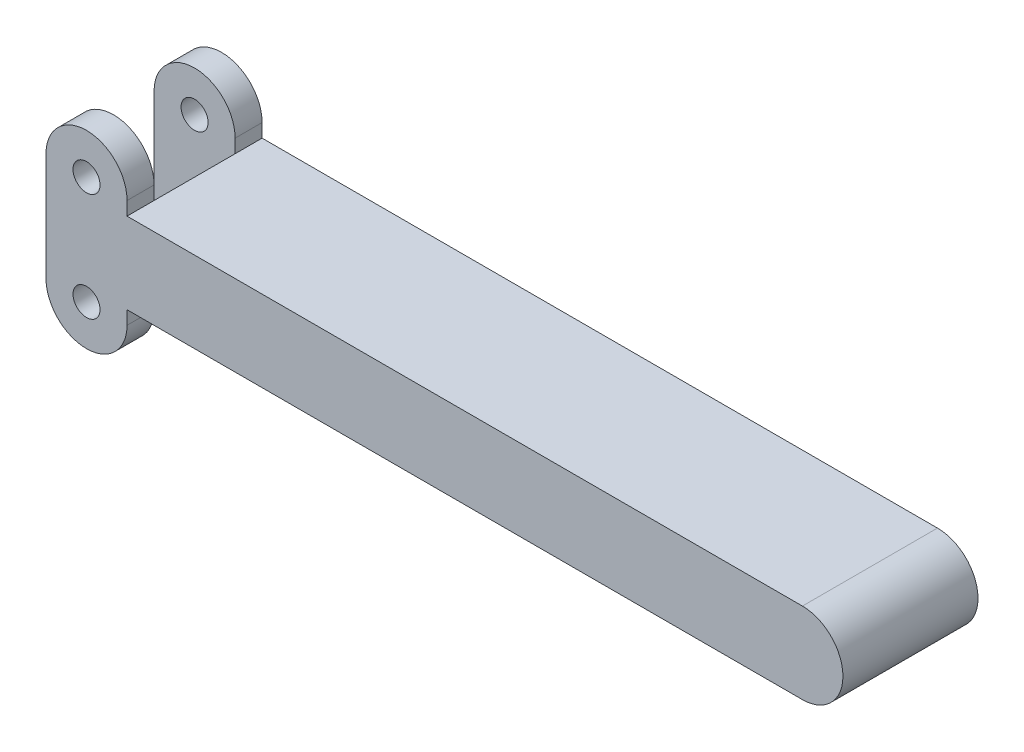
SolidWorks part; units mm, degrees
ref_plane "Front Plane" through (0, 0, 0) normal (0, 0, 1) x (1, 0, 0)
ref_plane "Top Plane" through (0, 0, 0) normal (0, 1, 0) x (1, 0, 0)
ref_plane "Right Plane" through (0, 0, 0) normal (1, 0, 0) x (0, 0, -1)
sketch "Sketch1" plane through (0, 0, 0) normal (0, 0, 1) x (1, 0, 0)
  line L0 (0, 0) -> (0, 25.4) construction
  line L1 (-9.525, 0) -> (-9.525, 25.4)
  line L2 (9.525, 0) -> (9.525, 25.4)
  line L3 (9.525, 22.225) -> (168.275, 22.225)
  line L4 (9.525, 3.175) -> (168.275, 3.175)
  line L5 (0, 12.7) -> (9.525, 22.225) construction
  line L6 (0, 12.7) -> (9.525, 3.175) construction
  arc A0 (-9.525, 0) -> (9.525, 0) centre (0, 0) ccw
  arc A1 (9.525, 25.4) -> (-9.525, 25.4) centre (0, 25.4) ccw
  arc A2 (168.275, 22.225) -> (168.275, 3.175) centre (168.275, 12.7) cw
  circle A3 centre (0, 25.4) radius 3.175
  circle A4 centre (0, 0) radius 3.175
  point P3 (0, 12.7)
  point P17 (9.525, 12.7)
  dimension "D1" = 9.525
  dimension "D5" = 6.35
  dimension "D2" = 25.4
  dimension "D3" = 19.05
  dimension "D6" = 158.75
extrude "Boss-Extrude1" add sketch "Sketch1" along normal blind 31.75
sketch "Sketch2" plane through (-9.525, 0, 0) normal (-1, 0, 0) x (0, 0, 1)
  line L0 (0, 0) -> (0, -9.525) construction
  line L1 (0, 0) -> (31.75, 0) construction
  line L2 (31.75, -9.525) -> (31.75, 0) construction
  line L3 (0, 34.925) -> (0, 25.4) construction
  line L4 (31.75, 25.4) -> (31.75, 34.925) construction
  line L5 (31.75, 25.4) -> (0, 25.4) construction
  line L6 (0, 25.4) -> (0, 0) construction
  line L7 (31.75, 0) -> (31.75, 25.4) construction
  line L8 (0, 0) -> (0, -9.525)
  line L9 (0, 0) -> (31.75, 0)
  line L10 (31.75, -9.525) -> (31.75, 0)
  line L11 (0, 34.925) -> (0, 25.4)
  line L12 (31.75, 25.4) -> (31.75, 34.925)
  line L13 (31.75, 25.4) -> (0, 25.4)
  line L14 (0, 25.4) -> (0, 0)
  line L15 (31.75, 0) -> (31.75, 25.4)
  line L16 (31.75, 34.925) -> (0, 34.925) construction
  line L17 (6.35, 34.925) -> (25.4, 34.925)
  line L18 (6.35, 34.925) -> (6.35, -9.525)
  line L19 (6.35, -9.525) -> (25.4, -9.525)
  line L20 (25.4, 34.925) -> (25.4, -9.525)
  line L21 (0, -9.525) -> (31.75, -9.525) construction
  dimension "D1" = 19.05
  dimension "D2" = 6.35
extrude "Cut-Extrude1" cut sketch "Sketch2" against normal blind 19.05 contours L20 L13 L18 L9 | L20 L17 L18 L13 | L20 L9 L18 L19
